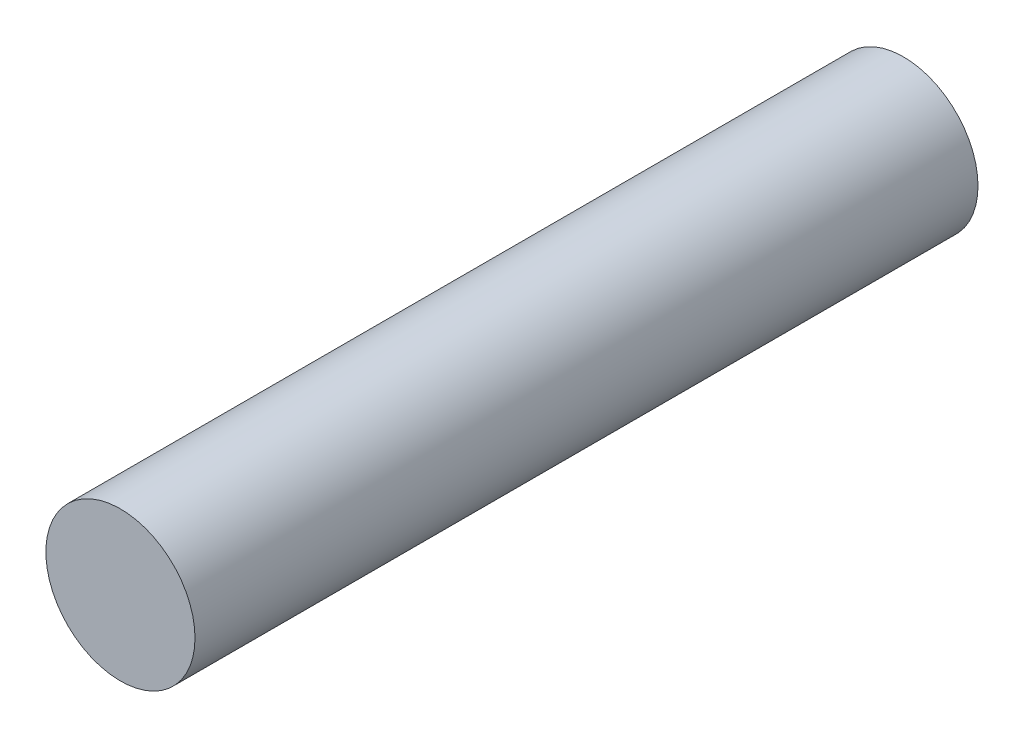
SolidWorks part; units mm, degrees
ref_plane "Front Plane" through (0, 0, 0) normal (0, 0, 1) x (1, 0, 0)
ref_plane "Top Plane" through (0, 0, 0) normal (0, 1, 0) x (1, 0, 0)
ref_plane "Right Plane" through (0, 0, 0) normal (1, 0, 0) x (0, 0, -1)
sketch "Sketch1" plane through (0, 0, 0) normal (0, 0, 1) x (1, 0, 0)
  circle A0 centre (0, 0) radius 2
  dimension "D1" = 4
extrude "Boss-Extrude1" add sketch "Sketch1" along normal blind 21
